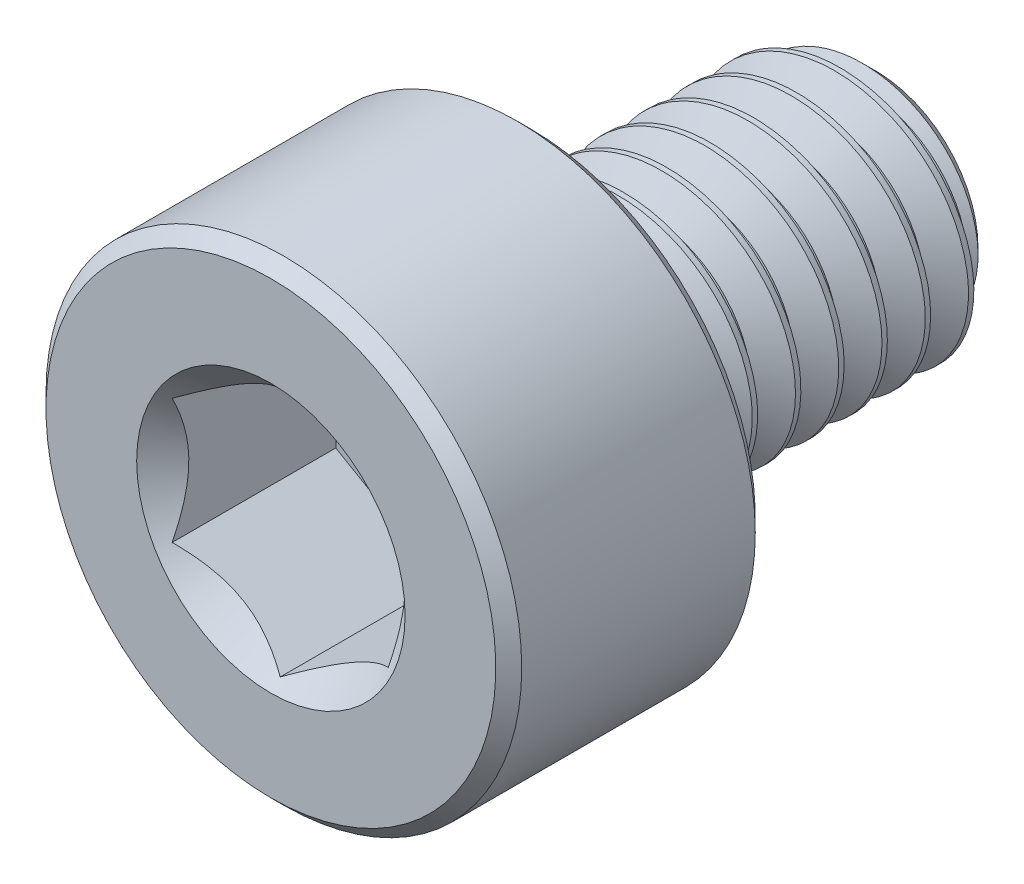
SolidWorks part; units mm, degrees
ref_plane "Front Plane" through (0, 0, 0) normal (0, 0, 1) x (1, 0, 0)
ref_plane "Top Plane" through (0, 0, 0) normal (0, 1, 0) x (1, 0, 0)
ref_plane "Right Plane" through (0, 0, 0) normal (1, 0, 0) x (0, 0, -1)
sketch "Sketch1" plane through (0, 0, 0) normal (1, 0, 0) x (0, 0, -1)
  line L0 (-3.5, 0) -> (3.5, 0) construction
  line L1 (3.5, 0) -> (3.5, 1.1752) construction
  line L2 (3.5, 1.1752) -> (3.1752, 1.5) construction
  line L3 (3.1752, 1.5) -> (3.125, 1.5) construction
  line L4 (3.125, 1.5) -> (-0.5, 1.5) construction
  line L5 (-0.5, 1.5) -> (-0.5, 2.75) construction
  line L6 (-0.5, 2.75) -> (-3.5, 2.75) construction
  line L7 (-3.5, 2.75) -> (-3.5, 0) construction
  line L8 (3.5, 1.1752) -> (3.5, 1.5) construction
  line L9 (3.4687, 1.5541) -> (3.7187, 1.1211) construction
  line L10 (3.7187, 1.1211) -> (3.9687, 1.5541) construction
  line L11 (3.9687, 1.5541) -> (3.4687, 1.5541) construction
  line L12 (3.7187, 1.5541) -> (3.7188, 1.5) construction
  line L13 (3.7187, 1.1211) -> (3.7187, 1.1752) construction
  line L14 (3.6875, 1.1752) -> (3.75, 1.1752) construction
  line L15 (3.5, 1.5) -> (3.9375, 1.5) construction
  line L16 (3.4844, 1.5271) -> (3.9531, 1.5271) construction
  line L17 (3.5, 0) -> (3.5, -1.5) construction
  line L18 (-0.65, 2.75) -> (-0.5, 2.6) construction
  line L19 (-3.35, 2.75) -> (-3.5, 2.6) construction
  line L20 (-0.5, 1.5) -> (-0.5, 0) construction
  line L21 (-0.5, 0.75) -> (0.8333, 0.75) construction
  line L22 (0.8333, 0.75) -> (2.1667, 0.75) construction
  line L23 (2.1667, 0.75) -> (3.5, 0.75) construction
  line L24 (0.8333, 0.75) -> (0.8333, 1.5) construction
  line L25 (0.8333, 1.5) -> (0.8333, 2.75) construction
  line L26 (2.1667, 0.75) -> (2.1667, 2.75) construction
  point P0 (-3.5, 1.25)
  point P3 (2.25, 1.5)
  point P4 (0, 0)
  point P18 (2.1667, 1.5)
  point P22 (3.7187, 1.1752)
  point P24 (3.125, 1.5)
  point P25 (3.7188, 1.5)
  point P28 (3.7187, 1.5271)
  point P29 (2.25, -1.5)
  point P30 (0.8333, 1.5)
  point P31 (-2, 2.75)
  point P37 (-1.025, 2.75)
  point P38 (-3.275, 2.75)
  point P45 (0.8333, 0.75)
  point P46 (2.1667, 0.75)
  dimension "D2" = 0.0625
  dimension "D7" = 0.15
  dimension "D8" = 0.15
  dimension "D9" = 0.15
  dimension "D10" = 0.075
  dimension "D11" = 0.375
  dimension "Drive Size" = 2.5
  dimension "Head Diameter" = 5.5
  dimension "Head Height" = 3
  dimension "Thread Pitch" = 0.5
  dimension "Thread Dia" = 3
  dimension "Length" = 4
  dimension "D12" = 0.375
  dimension "D4" = 1.25
  dimension "D3" = 45
sketch "Sketch2" plane through (0, 0, 0) normal (1, 0, 0) x (0, 0, -1)
  line L0 (-3.5, 0) -> (-3.5, 2.6)
  line L1 (-3.35, 2.75) -> (-0.65, 2.75)
  line L2 (-0.5, 2.6) -> (-0.5, 1.65)
  line L4 (3.1752, 1.5) -> (3.5, 1.1752)
  line L5 (3.5, 1.1752) -> (3.5, 0)
  line L6 (-0.5, 2.75) -> (-3.5, 2.75) construction
  line L7 (3.5, 0) -> (-3.5, 0)
  line L8 (-3.35, 2.75) -> (-3.5, 2.6) construction
  line L10 (-3.35, 2.75) -> (-3.5, 2.6)
  line L14 (-0.65, 2.75) -> (-0.5, 2.6) construction
  line L16 (-0.65, 2.75) -> (-0.5, 2.6)
  line L17 (-0.5, 1.5) -> (-0.5, 2.75) construction
  line L19 (-0.35, 1.5) -> (3.1752, 1.5)
  line L20 (3.125, 1.5) -> (-0.5, 1.5) construction
  arc A1 (-0.5, 1.65) -> (-0.35, 1.5) centre (-0.35, 1.65) ccw
  dimension "D3" = 0.15
revolve "Revolve1" add sketch "Sketch2" angle 360 about L7
sketch "Sketch3" plane through (0, 0, 3.5) normal (0, 0, 1) x (1, 0, 0)
  line L1 (1.25, -0.7217) -> (1.25, 0.7217)
  line L2 (1.25, 0.7217) -> (0, 1.4434)
  line L3 (0, 1.4434) -> (-1.25, 0.7217)
  line L4 (-1.25, 0.7217) -> (-1.25, -0.7217)
  line L5 (-1.25, -0.7217) -> (0, -1.4434)
  line L6 (0, -1.4434) -> (1.25, -0.7217)
  circle A0 centre (0, 0) radius 1.25 construction
  circle A1 centre (0, 0) radius 2.75 construction
  circle A2 centre (0, 0) radius 2.75 construction
  circle A3 centre (0, 0) radius 1.4434 construction
  point P13 (0, 0)
  dimension "D1" = 2.8868
extrude "Cut-Extrude1" cut sketch "Sketch3" against normal offset from surface (2 mm away) 1 up to face at (0, 2.6, 0.5)
sketch "Sketch4" plane through (0, 0, 3.5) normal (0, 0, 1) x (1, 0, 0)
  circle A0 centre (0, 0) radius 1.5516
  dimension "D1" = 3.1033
extrude "Cut-Extrude2" cut sketch "Sketch4" against normal up to vertex (1.5 mm away) draft 45 up to point (0, 2.75, 2)
sketch "Sketch11" plane through (0, 0, 0) normal (1, 0, 0) x (0, 0, -1)
  line L0 (-3.5, 0) -> (3.5, 0) construction
  line L1 (-3.5, 0) -> (3.5, 0) construction
  line L2 (0.25, 0) -> (0.25, 1.5) construction
  line L3 (3.125, 1.5) -> (-0.5, 1.5) construction
  line L4 (2.75, 0) -> (2.75, 1.5) construction
  line L6 (3.5, 1.1752) -> (3.5, 1.5) construction
  point P2 (0.25, 0)
  point P3 (2.75, 0)
  dimension "D1" = 0.75
  dimension "D2" = 0.75
sketch "Sketch6" plane through (0, 0, -3.5) normal (0, 0, -1) x (-1, 0, 0)
  circle A0 centre (0, 0) radius 1.5
curve "Helix/Spiral1" pitch 0.5 height 4.5 turns 9
sketch "Sketch10" plane through (0, 0, 0) normal (1, 0, 0) x (0, 0, -1)
  line L0 (-0.35, -2.75) -> (-0.35, 2.75)
  line L5 (-3.5, 0) -> (3.5, 0) construction
  line L6 (-0.35, 1.5) -> (-0.35, -1.5) construction
  point P3 (-0.35, 0)
split "Split1" trim tools "Sketch10" bodies to split 106 resulting bodies 114 115
sketch "Sketch7" plane through (0, 0, 0) normal (1, 0, 0) x (0, 0, -1)
  line L0 (3.4844, 1.5271) -> (3.9531, 1.5271)
  line L1 (3.9531, 1.5271) -> (3.75, 1.1752)
  line L2 (3.75, 1.1752) -> (3.6875, 1.1752)
  line L3 (3.6875, 1.1752) -> (3.4844, 1.5271)
sweep "Cut-Sweep1" cut profiles "Sketch7" path "Helix/Spiral1"
sketch "Sketch8" plane through (0, 0, 0) normal (1, 0, 0) x (0, 0, -1)
  line L0 (-0.5, 0) -> (-0.5, 1.5)
  line L1 (-0.35, -1.5) -> (-0.35, 1.5) construction
  line L2 (-0.5, 1.5) -> (-0.35, 1.5)
  line L4 (-0.35, 1.5) -> (0.516, 0)
  line L5 (0.516, 0) -> (-0.5, 0)
  line L6 (3.125, 1.5) -> (-0.5, 1.5) construction
  line L7 (-3.5, 0) -> (3.5, 0) construction
  dimension "D1" = 60
revolve "Revolve2" add sketch "Sketch8" angle 360 about L5
equation "\"D2@Sketch1\" = \"Thread Pitch@Sketch1\" / 8"
equation "\"D4@Helix/Spiral1\" = \"Thread Pitch@Sketch1\""
equation "\"D7@Sketch1\" = \"Head Height@Sketch1\" * .05"
equation "\"D8@Sketch1\"=\"D7@Sketch1\""
equation "\"D9@Sketch1\"=\"D7@Sketch1\""
equation "\"D10@Sketch1\"=\"D7@Sketch1\"/2"
equation "\"D11@Sketch1\"=\"D10@Sketch1\"*5"
equation "\"D4@Sketch1\"=\"Thread Pitch@Sketch1\"*2.5"
equation "\"D12@Sketch1\"=\"Thread Pitch@Sketch1\"*.75"
equation "\"D3@Helix/Spiral1\"=\"Length@Sketch1\"+\"Thread Pitch@Sketch1\""
equation "\"D3@Sketch2\"=\"Thread Dia@Sketch1\"*0.05"
equation "\"D1@Sketch11\"=\"Length@Sketch1\"*0.1875"
equation "\"D2@Sketch11\"=\"D1@Sketch11\""
equation "\"D1@Sketch4\"=\"D1@Sketch3\"*1.075"
